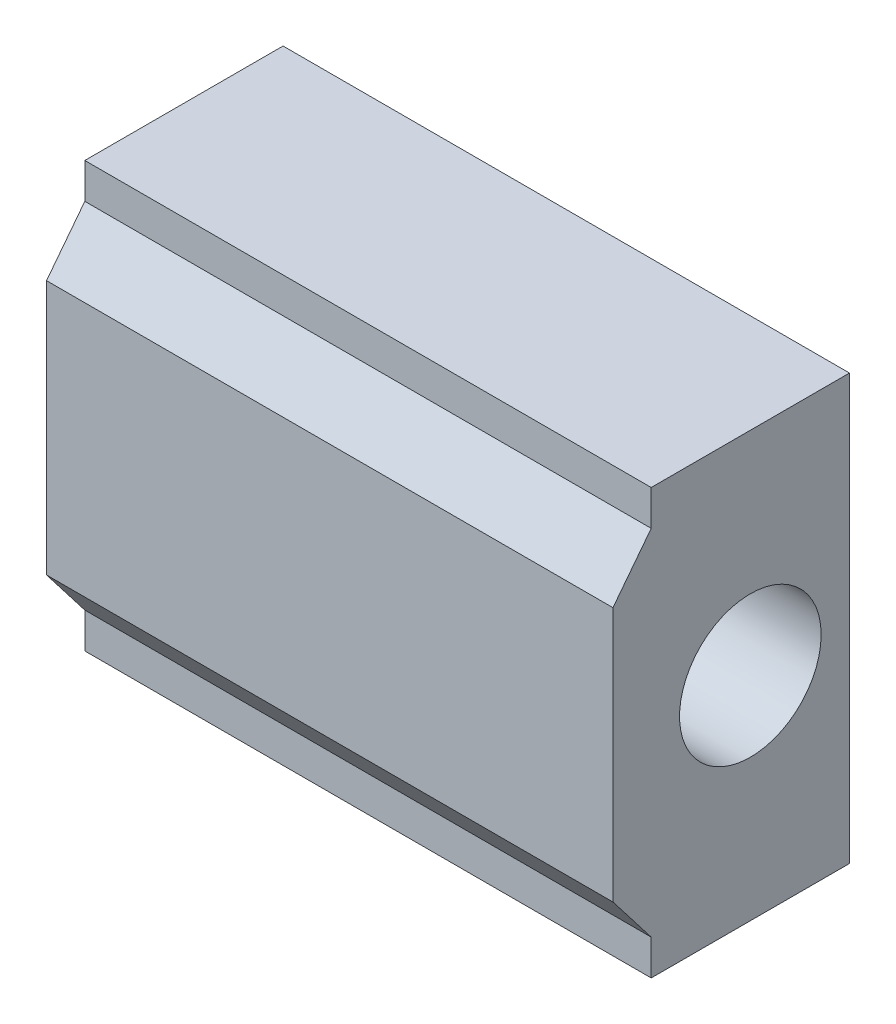
SolidWorks part; units mm, degrees
ref_plane "Front Plane" through (0, 0, 0) normal (0, 0, 1) x (1, 0, 0)
ref_plane "Top Plane" through (0, 0, 0) normal (0, 1, 0) x (1, 0, 0)
ref_plane "Right Plane" through (0, 0, 0) normal (1, 0, 0) x (0, 0, -1)
sketch "Sketch1" plane through (0, 0, 0) normal (1, 0, 0) x (0, 0, -1)
  line L1 (-9.7025, -9) -> (-9.7025, 9)
  line L2 (-9.7025, 9) -> (-7, 12.5)
  line L3 (-7, 12.5) -> (-7, 15)
  line L4 (-7, 15) -> (7, 15)
  line L5 (7, 15) -> (7, -15)
  line L6 (9.1864, 0) -> (-9.1864, 0) construction
  line L7 (-7, -15) -> (7, -15)
  line L8 (-7, -12.5) -> (-7, -15)
  line L9 (-9.7025, -9) -> (-7, -12.5)
  circle A0 centre (0, 0) radius 5
  point P12 (7, 0)
  point P15 (-9.7025, 0)
  dimension "D1" = 10
  dimension "D2" = 30
  dimension "D3" = 14
  dimension "D4" = 18
  dimension "D5" = 25
  dimension "D6" = 7
extrude "Boss-Extrude1" add sketch "Sketch1" along normal blind 40
